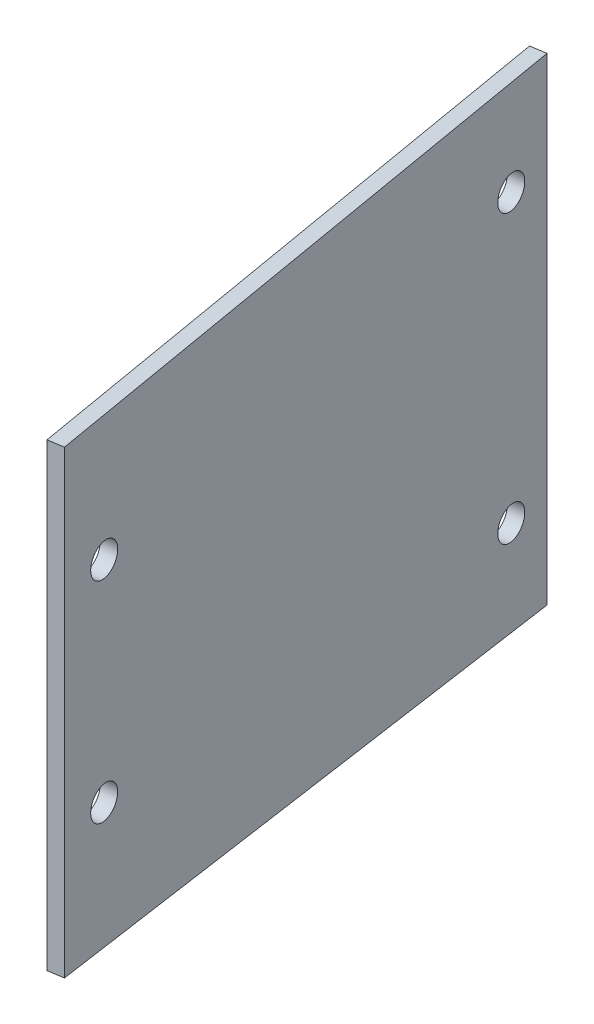
SolidWorks part; units mm, degrees
ref_plane "Front Plane" through (0, 0, 0) normal (0, 0, 1) x (1, 0, 0)
ref_plane "Top Plane" through (0, 0, 0) normal (0, 1, 0) x (1, 0, 0)
ref_plane "Right Plane" through (0, 0, 0) normal (1, 0, 0) x (0, 0, -1)
sketch "Sketch1" plane through (-29.0197, 0, 4.5948) normal (0.9877, 0, -0.1564) x (-0.1564, 0, -0.9877)
  line L0 (-6.5204, 24.0561) -> (54.227, 25)
  line L1 (54.227, 25) -> (54.227, -25)
  line L2 (54.227, -25) -> (-6.5204, -24.0561)
  line L3 (-6.5204, -24.0561) -> (-6.5204, 24.0561)
extrude "Boss-Extrude1" add sketch "Sketch1" along normal blind 1.6
sketch "Back Mounting Holes" plane through (-29.0197, 0, 4.5948) normal (-0.9877, 0, 0.1564) x (0.1564, 0, 0.9877)
  line L0 (1.5204, -24.1337) -> (1.5204, 24.1337) construction
  line L1 (6.5204, -24.0561) -> (-54.227, -25) construction
  line L2 (-54.227, 25) -> (6.5204, 24.0561) construction
  line L3 (0.8122, 0) -> (-49999.1878, 0) construction
  line L4 (6.5204, 24.0561) -> (6.5204, -24.0561) construction
  circle A0 centre (1.5204, -11) radius 1.7
  circle A1 centre (1.5204, 11) radius 1.7
  point P8 (1.5204, 0)
  dimension "D1" = 3.4
  dimension "D2" = 11
  dimension "D3" = 5
sketch "Front Mounting Holes" plane through (-29.0197, 0, 4.5948) normal (-0.9877, 0, 0.1564) x (0.1564, 0, 0.9877)
  line L0 (0, 0) -> (-50000, 0) construction
  line L2 (-49.727, -15) -> (-49.727, 15) construction
  line L3 (-54.227, -25) -> (-54.227, 25) construction
  circle A1 centre (-49.727, 15) radius 1.7
  circle A2 centre (-49.727, -15) radius 1.7
  point P6 (-49.727, 0)
  dimension "D1" = 3.4
  dimension "D2" = 3.4
  dimension "D3" = 4.5
  dimension "D4" = 15
extrude "Cut-Extrude1" cut sketch "Back Mounting Holes" against normal through all
extrude "Cut-Extrude2" cut sketch "Front Mounting Holes" against normal through all
sketch "PCB Sketch" plane through (-27.4394, 0, 4.3446) normal (0.9877, 0, -0.1564) x (-0.1564, 0, -0.9877)
  line L4 (-6.5204, 24.0561) -> (-6.5204, -24.0561)
  line L5 (-6.5204, -24.0561) -> (54.227, -25)
  line L6 (54.227, -25) -> (54.227, 25)
  line L7 (54.227, 25) -> (-6.5204, 24.0561)
  line L8 (-6.5204, 24.0561) -> (-6.5204, -24.0561)
  line L9 (-6.5204, -24.0561) -> (54.227, -25)
  line L10 (54.227, -25) -> (54.227, 25)
  line L11 (54.227, 25) -> (-6.5204, 24.0561)
  circle A0 centre (49.727, -15) radius 1.7 construction
  circle A1 centre (49.727, 15) radius 1.7 construction
  circle A2 centre (-1.5204, -11) radius 1.7 construction
  circle A3 centre (-1.5204, 11) radius 1.7 construction
  circle A4 centre (49.727, -15) radius 1.7
  circle A5 centre (49.727, 15) radius 1.7
  circle A6 centre (-1.5204, -11) radius 1.7
  circle A7 centre (-1.5204, 11) radius 1.7
  dimension "D1" = 0
